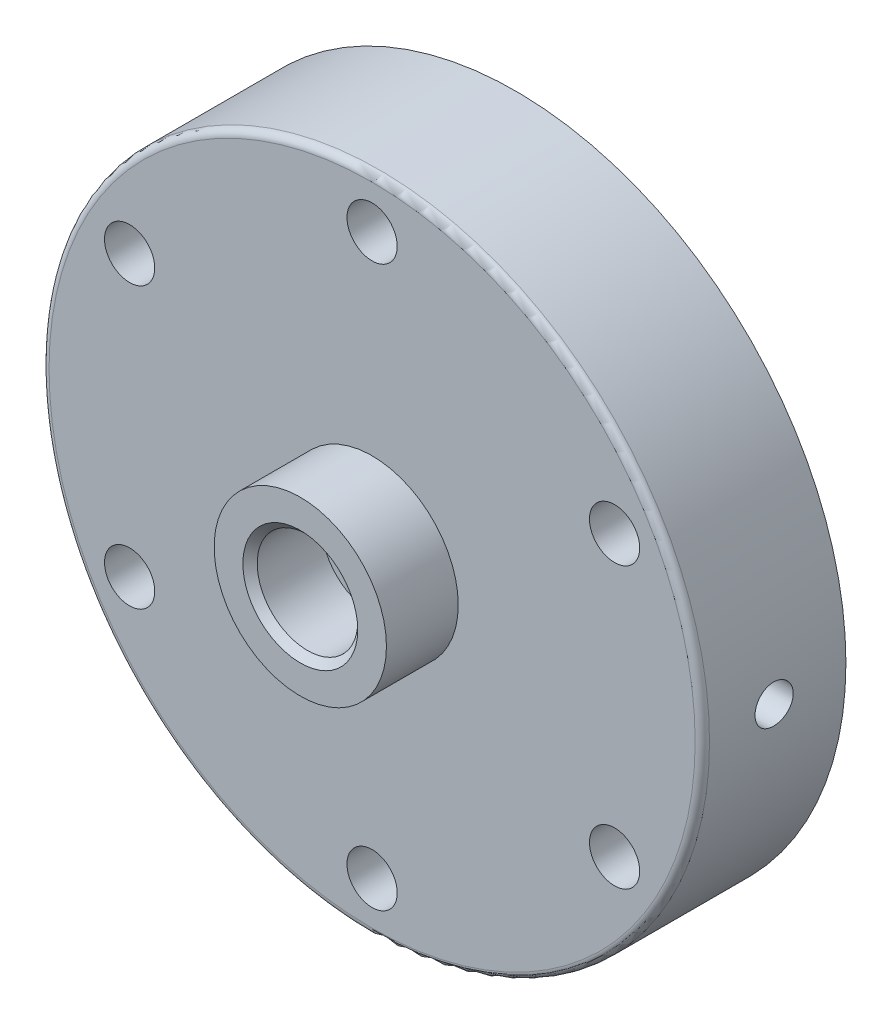
SolidWorks part; units mm, degrees
ref_plane "Front Plane" through (0, 0, 0) normal (0, 0, 1) x (1, 0, 0)
ref_plane "Top Plane" through (0, 0, 0) normal (0, 1, 0) x (1, 0, 0)
ref_plane "Right Plane" through (0, 0, 0) normal (1, 0, 0) x (0, 0, -1)
sketch "Sketch2" plane through (0, 0, 0) normal (0, 0, 1) x (1, 0, 0)
  circle A0 centre (0, 0) radius 46
  circle A1 centre (0, 0) radius 39 construction
  circle A2 centre (0, 39) radius 3.5
  circle A3 centre (0, 0) radius 2.5
  circle A4 centre (33.775, 19.5) radius 3.5
  circle A5 centre (33.775, -19.5) radius 3.5
  circle A6 centre (0, -39) radius 3.5
  circle A7 centre (-33.775, -19.5) radius 3.5
  circle A8 centre (-33.775, 19.5) radius 3.5
  point P20 (0, 0)
  dimension "D1" = 92
  dimension "D2" = 78
  dimension "D3" = 7
  dimension "D4" = 5
  dimension "D5" = 6
extrude "Boss-Extrude1" add sketch "Sketch2" along normal blind 20
sketch "Sketch3" plane through (0, 0, 20) normal (0, 0, 1) x (1, 0, 0)
  circle A0 centre (0, 0) radius 12
  circle A1 centre (0, 0) radius 7
  dimension "D1" = 24
  dimension "D2" = 14
extrude "Boss-Extrude2" add sketch "Sketch3" along normal blind 10
cosmetic thread "Cosmetic Thread1" parameters "D2"=16
chamfer "Chamfer1" distance 1 angle 45 1 edges at (7, 0, 30)
sketch "Sketch6" plane through (0, 0, 0) normal (0, 0, -1) x (-1, 0, 0)
  circle A0 centre (0, 0) radius 33
  dimension "D1" = 66
extrude "Cut-Extrude1" cut sketch "Sketch6" against normal blind 14
fillet "Fillet1" radius 1 1 edges at (46, 0, 20)
sketch "Sketch7" plane through (0, 0, 0) normal (1, 0, 0) x (0, 0, -1)
  circle A0 centre (-10, 0) radius 2.6602
  point P2 (0, 0)
  point P4 (0, 0)
  point P7 (0, 0)
  dimension "D1" = 10
extrude "Cut-Extrude2" cut sketch "Sketch7" against normal through all both and the other way through all
